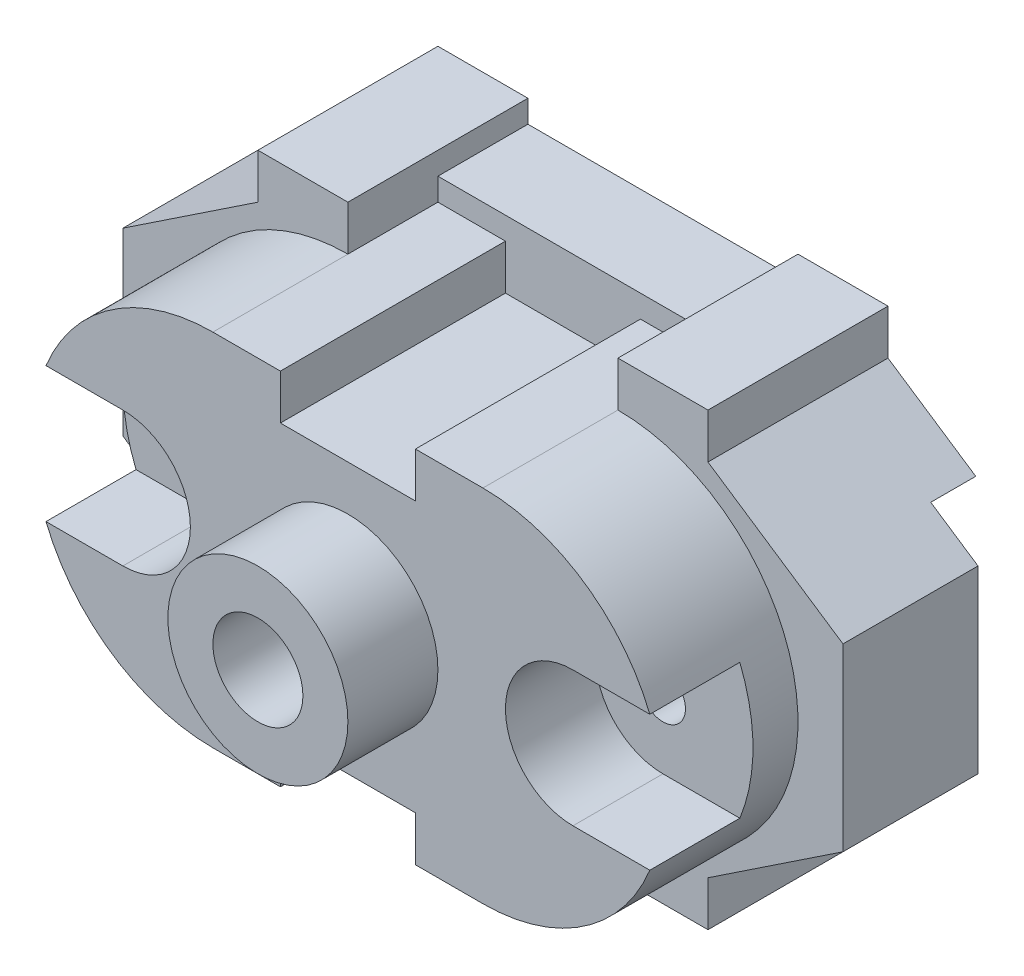
SolidWorks part; units mm, degrees
ref_plane "Front Plane" through (0, 0, 0) normal (0, 0, 1) x (1, 0, 0)
ref_plane "Top Plane" through (0, 0, 0) normal (0, 1, 0) x (1, 0, 0)
ref_plane "Right Plane" through (0, 0, 0) normal (1, 0, 0) x (0, 0, -1)
sketch "Sketch1" plane through (0, 0, 0) normal (0, 0, 1) x (1, 0, 0)
  line L0 (0, 40.887) -> (-20, 40.887)
  line L1 (-20, 40.887) -> (-20, 30.887)
  line L2 (-20, 30.887) -> (-50, 10.887)
  line L3 (-50, 10.887) -> (-50, -29.113)
  line L4 (-50, -29.113) -> (-20, -49.113)
  line L5 (-20, -49.113) -> (-20, -59.113)
  line L6 (-20, -59.113) -> (0, -59.113)
  line L7 (0, -59.113) -> (0, -54.113)
  line L8 (80, -59.113) -> (60, -59.113)
  line L9 (0, -54.113) -> (60, -54.113)
  line L10 (60, -54.113) -> (60, -59.113)
  line L11 (80, -59.113) -> (80, -49.113)
  line L12 (80, -49.113) -> (110, -29.113)
  line L13 (110, -29.113) -> (110, 10.887)
  line L14 (110, 10.887) -> (80, 30.887)
  line L15 (80, 30.887) -> (80, 40.887)
  line L16 (80, 40.887) -> (60, 40.887)
  line L17 (60, 40.887) -> (60, 35.887)
  line L18 (60, 35.887) -> (0, 35.887)
  line L19 (0, 35.887) -> (0, 40.887)
  dimension "D1" = 20
  dimension "D2" = 20
  dimension "D3" = 5
  dimension "D4" = 5
  dimension "D5" = 60
  dimension "D6" = 10
  dimension "D7" = 10
  dimension "D8" = 30
  dimension "D9" = 20
  dimension "D10" = 30
  dimension "D11" = 20
  dimension "D12" = 40
  dimension "D13" = 40
  dimension "D14" = 20
  dimension "D15" = 30
  dimension "D16" = 10
  dimension "D17" = 20
  dimension "D18" = 5
  dimension "D19" = 30
  dimension "D20" = 20
  dimension "D21" = 10
  dimension "D22" = 20
  dimension "D23" = 5
  dimension "D24" = 54.113
extrude "Boss-Extrude1" add sketch "Sketch1" along normal blind 40
sketch "Sketch2" plane through (0, 0, 40) normal (0, 0, 1) x (1, 0, 0)
  line L0 (0, 30.887) -> (15, 30.887)
  line L1 (15, 30.887) -> (15, 20.887)
  line L2 (15, 20.887) -> (45, 20.887)
  line L3 (45, 20.887) -> (45, 30.887)
  line L4 (60, 30.887) -> (45, 30.887)
  line L5 (-50, 10.887) -> (-50, -29.113) construction
  line L6 (0, -49.113) -> (15, -49.113)
  line L7 (15, -49.113) -> (15, -39.113)
  line L8 (15, -39.113) -> (45, -39.113)
  line L9 (45, -39.113) -> (45, -49.113)
  line L10 (45, -49.113) -> (60, -49.113)
  arc A0 (0, 30.887) -> (0, -49.113) centre (0, -9.113) ccw
  arc A1 (60, 30.887) -> (60, -49.113) centre (60, -9.113) cw
  dimension "D1" = 40
  dimension "D2" = 40
  dimension "D7" = 15
  dimension "D3" = 5
  dimension "D4" = 5
  dimension "D5" = 5
  dimension "D6" = 5
  dimension "D8" = 15
  dimension "D9" = 30
  dimension "D10" = 10
  dimension "D11" = 50
  dimension "D12" = 15
  dimension "D13" = 15
  dimension "D14" = 10
extrude "Boss-Extrude2" add sketch "Sketch2" along normal blind 30
sketch "Sketch3" plane through (0, 0, 70) normal (0, 0, 1) x (1, 0, 0)
  line L0 (-50, 10.887) -> (-50, -29.113) construction
  circle A0 centre (30, -9.113) radius 20
  dimension "D1" = 40
  dimension "D2" = 80
  dimension "D3" = 50
extrude "Boss-Extrude3" add sketch "Sketch3" along normal blind 20
sketch "Sketch4" plane through (0, 0, 90) normal (0, 0, 1) x (1, 0, 0)
  circle A0 centre (30, -9.113) radius 10
  dimension "D1" = 20
extrude "Cut-Extrude1" cut sketch "Sketch4" against normal blind 185
sketch "Sketch5" plane through (0, 0, 70) normal (0, 0, 1) x (1, 0, 0)
  line L0 (110, -29.113) -> (110, 10.887) construction
  line L1 (-50, 10.887) -> (-50, -29.113) construction
  circle A0 centre (-20, -9.113) radius 5
  circle A1 centre (80, -9.113) radius 5
  point P6 (-50, -9.113)
  dimension "D1" = 10
  dimension "D2" = 10
  dimension "D3" = 30
  dimension "D4" = 30
  dimension "D5" = 50
  dimension "D6" = 50
extrude "Cut-Extrude2" cut sketch "Sketch5" against normal blind 185
sketch "Sketch6" plane through (0, 0, 70) normal (0, 0, 1) x (1, 0, 0)
  line L0 (-20, 5.887) -> (-37.081, 5.887)
  line L1 (-20, -24.113) -> (-37.081, -24.113)
  line L2 (80, 5.887) -> (97.081, 5.887)
  line L3 (80, -24.113) -> (97.081, -24.113)
  arc A0 (-20, 5.887) -> (-20, -24.113) centre (-20, -9.113) cw
  arc A1 (80, 5.887) -> (80, -24.113) centre (80, -9.113) ccw
  arc A2 (0, 30.887) -> (0, -49.113) centre (0, -9.113) ccw construction
  arc A3 (60, -49.113) -> (60, 30.887) centre (60, -9.113) ccw construction
  arc A4 (-37.081, 5.887) -> (-37.081, -24.113) centre (0, -9.113) ccw
  arc A5 (97.081, 5.887) -> (97.081, -24.113) centre (60, -9.113) cw
  circle M1 centre (80, -9.113) radius 5
  circle M2 centre (-20, -9.113) radius 5
  arc M3 (0, 30.887) -> (0, -49.113) centre (0, -9.113) ccw
  arc M9 (60, -49.113) -> (60, 30.887) centre (60, -9.113) ccw
  dimension "D1" = 15
  dimension "D2" = 15
extrude "Cut-Extrude3" cut sketch "Sketch6" against normal blind 20 contours A0 L0 L1 M3 M2 | L2 A1 L3 M9 M1
sketch "Sketch7" plane through (0, 0, 40) normal (0, 0, 1) x (1, 0, 0)
  line L0 (0, 35.887) -> (0, 30.887)
  line L1 (0, 30.887) -> (15, 30.887)
  line L2 (15, 30.887) -> (15, 20.887)
  line L3 (15, 20.887) -> (45, 20.887)
  line L4 (45, 20.887) -> (45, 30.887)
  line L5 (45, 30.887) -> (60, 30.887)
  line L6 (60, 30.887) -> (60, 35.887)
  line L7 (60, 35.887) -> (0, 35.887)
extrude "Cut-Extrude4" cut sketch "Sketch7" against normal blind 20
sketch "Sketch8" plane through (0, 0, 40) normal (0, 0, 1) x (1, 0, 0)
  line L0 (0, -54.113) -> (0, -49.113)
  line L1 (0, -49.113) -> (15, -49.113)
  line L2 (15, -49.113) -> (15, -39.113)
  line L3 (15, -39.113) -> (45, -39.113)
  line L4 (45, -39.113) -> (45, -49.113)
  line L5 (45, -49.113) -> (60, -49.113)
  line L6 (60, -49.113) -> (60, -54.113)
  line L7 (60, -54.113) -> (0, -54.113)
extrude "Cut-Extrude5" cut sketch "Sketch8" against normal blind 20
sketch "Sketch9" plane through (0, 0, 0) normal (0, 0, -1) x (-1, 0, 0)
  line L0 (-99.5, 17.887) -> (39.5, 17.887)
  line L1 (-110, 10.887) -> (-80, 30.887) construction
  line L2 (20, 30.887) -> (50, 10.887) construction
  line L3 (-99.5, -36.113) -> (39.5, -36.113)
  line L4 (-80, -49.113) -> (-110, -29.113) construction
  line L5 (50, -29.113) -> (20, -49.113) construction
  line L6 (39.5, 17.887) -> (50, 10.887)
  line L7 (50, 10.887) -> (50, -29.113)
  line L8 (50, -29.113) -> (39.5, -36.113)
  line L9 (-99.5, -36.113) -> (-110, -29.113)
  line L10 (-110, -29.113) -> (-110, 10.887)
  line L11 (-110, 10.887) -> (-99.5, 17.887)
  dimension "D1" = 7
  dimension "D2" = 7
extrude "Cut-Extrude7" cut sketch "Sketch9" against normal blind 10
